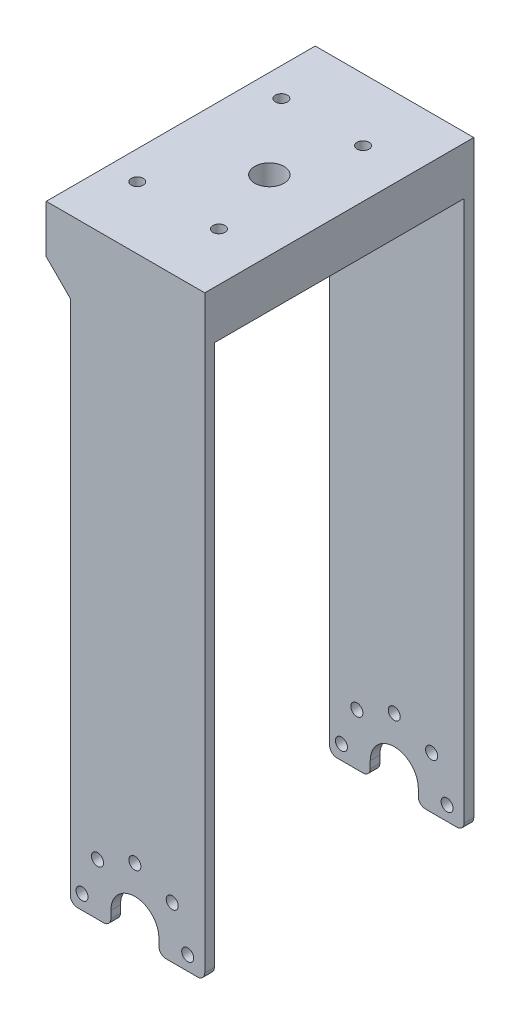
SolidWorks part; units mm, degrees
ref_plane "Front Plane" through (0, 0, 0) normal (0, 0, 1) x (1, 0, 0)
ref_plane "Top Plane" through (0, 0, 0) normal (0, 1, 0) x (1, 0, 0)
ref_plane "Right Plane" through (0, 0, 0) normal (1, 0, 0) x (0, 0, -1)
sketch "Sketch1" plane through (0, 0, 0) normal (0, 0, 1) x (1, 0, 0)
  line L1 (0, 0) -> (28, 0)
  line L2 (0, 0) -> (0, 124.1)
  line L3 (0, 124.1) -> (28, 124.1)
  line L4 (28, 0) -> (28, 124.1)
  dimension "D1" = 28
  dimension "D2" = 124.1
extrude "Boss-Extrude1" add sketch "Sketch1" against normal blind 2
ref_plane "Plane1" through (0, 0, -56) normal (0, 0, 1) x (1, 0, 0)
sketch "Sketch3" plane through (0, 0, 0) normal (0, 0, 1) x (1, 0, 0)
  line L0 (0, 0) -> (28, 0) construction
  line L2 (8.45, 3) -> (8.45, 0)
  line L3 (18.45, 3) -> (18.45, 0)
  arc A0 (18.45, 3) -> (8.45, 3) centre (13.45, 3) ccw
  dimension "D1" = 10
  dimension "D2" = 3
extrude "Cut-Extrude2" cut sketch "Sketch3" against normal blind 2 and the other way through all flip side to cut
ref_point "Point1"
ref_axis "Axis1" through (13.45, 3, 0) along (0, 0, -1)
sketch "Sketch4" plane through (0, 0, 0) normal (0, 0, 1) x (1, 0, 0)
  line L0 (0, 0) -> (8.45, 0) construction
  circle A0 centre (2.45, 3) radius 1.25
  arc A1 (18.45, 3) -> (8.45, 3) centre (13.45, 3) ccw construction
  dimension "D1" = 2.5
  dimension "D2" = 3
  dimension "D3" = 11
extrude "Cut-Extrude3" cut sketch "Sketch4" against normal blind 2
pattern_circular "CirPattern1" count 5 every 45 about axis through (13.45, 3, 0) along (0, 0, 1) of "Cut-Extrude3"
fillet "Fillet1" radius 1.5 4 edges at (28, 0, -1) (0, 0, -1) (18.45, 0, -1) (8.45, 0, -1)
sketch "Sketch7" plane through (0, 0, -56) normal (0, 0, 1) x (1, 0, 0)
  line L1 (0, 0) -> (28, 0)
  line L2 (0, 0) -> (0, 124.1)
  line L3 (0, 124.1) -> (28, 124.1)
  line L4 (28, 0) -> (28, 124.1)
  dimension "D1" = 28
  dimension "D2" = 124.1
extrude "Boss-Extrude2" add sketch "Sketch7" along normal blind 2 separate body
ref_point "Point2"
sketch "Sketch10" plane through (0, 0, -56) normal (0, 0, -1) x (-1, 0, 0)
  line L1 (-18.45, 3) -> (-18.45, 0)
  line L2 (0, 0) -> (-28, 0) construction
  line L3 (-8.45, 3) -> (-8.45, 0)
  arc A0 (-8.45, 3) -> (-18.45, 3) centre (-13.45, 3) ccw
  dimension "D1" = 10
extrude "Cut-Extrude4" cut sketch "Sketch10" against normal blind 2 and the other way through all flip side to cut
sketch "Sketch11" plane through (0, 0, -56) normal (0, 0, -1) x (-1, 0, 0)
  circle A0 centre (-24.45, 3) radius 1.25
  arc A1 (-8.45, 3) -> (-18.45, 3) centre (-13.45, 3) ccw construction
  dimension "D1" = 2.5
  dimension "D2" = 11
extrude "Cut-Extrude5" cut sketch "Sketch11" against normal blind 2
pattern_circular "CirPattern2" count 5 over 180 about axis through (13.45, 3, 0) along (0, 0, 1) of "Cut-Extrude5"
fillet "Fillet2" radius 1.5 4 edges at (28, 0, -55) (0, 0, -55) (8.45, 0, -55) (18.45, 0, -55)
sketch "Sketch17" plane through (0, 124.1, 0) normal (0, 1, 0) x (1, 0, 0)
  line L1 (28, 2) -> (-5, 2)
  line L2 (28, 2) -> (28, 54)
  line L3 (28, 54) -> (-5, 54)
  line L4 (-5, 2) -> (-5, 54)
  dimension "D1" = 52
  dimension "D2" = 33
extrude "Boss-Extrude5" add sketch "Sketch17" against normal blind 15
sketch "Sketch18" plane through (0, 124.1, 0) normal (0, 1, 0) x (1, 0, 0)
  line L1 (-5, 2) -> (0, 2) construction
  circle A0 centre (13.45, 28) radius 3.05
  dimension "D1" = 6.1
  dimension "D2" = 26
extrude "Cut-Extrude7" cut sketch "Sketch18" against normal up to next
sketch "Sketch19" plane through (0, 124.1, 0) normal (0, 1, 0) x (1, 0, 0)
  circle A0 centre (0.95, 43) radius 1.25
  circle A1 centre (13.45, 28) radius 3.05 construction
  circle A2 centre (17.95, 43) radius 1.25
  dimension "D1" = 2.5
  dimension "D2" = 15
  dimension "D3" = 12.5
  dimension "D4" = 2.5
  dimension "D5" = 17
  dimension "D6" = 15
extrude "Cut-Extrude8" cut sketch "Sketch19" against normal blind 10
ref_plane "Plane4" through (0, 0, -28) normal (0, 0, -1) x (-1, 0, 0)
mirror "Mirror9" about plane through (0, 0, -28) normal (0, 0, -1) of "Cut-Extrude8"
sketch "Sketch20" plane through (0, 109.1, 0) normal (0, -1, 0) x (1, 0, 0)
  line L0 (28, -54) -> (0, -54) construction
  line L1 (26.05, -54) -> (-3.05, -54)
  line L2 (26.05, -54) -> (26.05, -2)
  line L3 (26.05, -2) -> (-3.05, -2)
  line L4 (-3.05, -54) -> (-3.05, -2)
  line L6 (28, -2) -> (28, -54) construction
  circle A1 centre (0.95, -43) radius 1.25 construction
  dimension "D1" = 52
  dimension "D2" = 1.95
  dimension "D3" = 4
extrude "Cut-Extrude9" cut sketch "Sketch20" against normal blind 5
sketch "Sketch21" plane through (0, 0, -2) normal (0, 0, 1) x (1, 0, 0)
  line L0 (0, 114.1) -> (0, 1.5) construction
  line L1 (-5, 124.1) -> (0, 124.1)
  line L2 (-5, 124.1) -> (-5, 109.1)
  line L3 (-5, 109.1) -> (0, 109.1)
  line L4 (0, 124.1) -> (0, 109.1)
extrude "Boss-Extrude6" add sketch "Sketch21" along normal blind 2
mirror "Mirror10" about plane through (0, 0, -28) normal (0, 0, -1) of "Boss-Extrude6"
sketch "Sketch22" plane through (26.05, 0, 0) normal (-1, 0, 0) x (0, 0, 1)
  line L0 (-54, 114.1) -> (-2, 114.1) construction
  line L1 (-2, 114.1) -> (-54, 114.1)
  line L2 (-2, 114.1) -> (-2, 109.1)
  line L3 (-2, 109.1) -> (-54, 109.1)
  line L4 (-54, 114.1) -> (-54, 109.1)
extrude "Cut-Extrude10" cut sketch "Sketch22" against normal through all
sketch "Sketch23" plane through (-3.05, 0, 0) normal (1, 0, 0) x (0, 0, -1)
  line L1 (2, 114.1) -> (54, 114.1)
  line L2 (2, 114.1) -> (2, 109.1)
  line L3 (2, 109.1) -> (54, 109.1)
  line L4 (54, 114.1) -> (54, 109.1)
extrude "Cut-Extrude11" cut sketch "Sketch23" against normal through all
sketch "Sketch24" plane through (0, 0, -2) normal (0, 0, -1) x (-1, 0, 0)
  line L0 (0, 109.1) -> (5, 114.1)
  line L1 (-28, 114.1) -> (5, 114.1) construction
  line L2 (5, 114.1) -> (5, 109.1)
  line L3 (5, 109.1) -> (0, 109.1) construction
  line L4 (5, 114.1) -> (5, 109.1) construction
  line L5 (5, 109.1) -> (0, 109.1)
extrude "Cut-Extrude12" cut sketch "Sketch24" against normal through all
mirror "Mirror11" about plane through (0, 0, -28) normal (0, 0, -1) of "Cut-Extrude12"
sketch "Sketch25" plane through (0, 114.1, 0) normal (0, -1, 0) x (1, 0, 0)
  circle A0 centre (0.95, -43) radius 2.5
  circle A1 centre (17.95, -43) radius 2.5
  dimension "D1" = 5
  dimension "D2" = 5
extrude "Cut-Extrude13" cut sketch "Sketch25" against normal blind 5
mirror "Mirror12" about plane through (0, 0, -28) normal (0, 0, -1) of "Cut-Extrude13"
